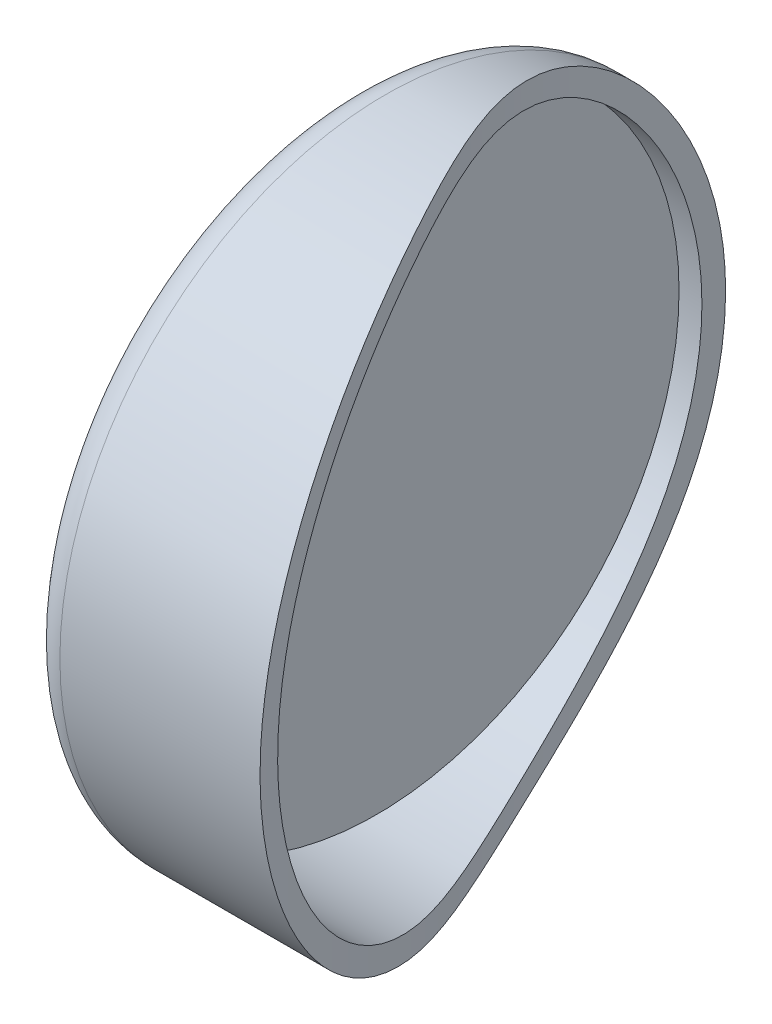
SolidWorks part; units mm, degrees
ref_plane "Front Plane" through (0, 0, 0) normal (0, 0, 1) x (1, 0, 0)
ref_plane "Top Plane" through (0, 0, 0) normal (0, 1, 0) x (1, 0, 0)
ref_plane "Right Plane" through (0, 0, 0) normal (1, 0, 0) x (0, 0, -1)
sketch "Sketch1" plane through (0, 0, 0) normal (1, 0, 0) x (0, 0, -1)
  circle A0 centre (0, 0) radius 70
  dimension "D1" = 140
extrude "Boss-Extrude1" add sketch "Sketch1" along normal blind 50
sketch "Sketch3" plane through (50, 0, 0) normal (1, 0, 0) x (0, 0, -1)
  circle A0 centre (0, 0) radius 65
  dimension "130" = 130
extrude "Cut-Extrude1" cut sketch "Sketch3" against normal blind 45
sketch "Sketch4" plane through (0, 0, 0) normal (0, 1, 0) x (1, 0, 0)
  line L1 (50, 70) -> (0, 70) construction
  line L2 (50, -70) -> (50, 70)
  line L3 (50, 70) -> (10, 70)
  spline S0 degree 3 poles (10, 70) (8.7362, 29.1132) (29.4581, -5.5685) (46.8115, -55.9434) (50, -70) knots 0 0 0 0 0.596241 1 1 1 1
  dimension "D2" = 146.8085
  dimension "D1" = 10
  dimension "D3" = 17.7508
extrude "Cut-Extrude2" cut sketch "Sketch4" against normal mid plane 165
fillet "Fillet2" radius 7 1 edges at (0, 0, -70)
sketch "Sketch5" plane through (0, 0, 0) normal (-1, 0, 0) x (0, 0, 1)
  circle A0 centre (0, 0) radius 50
  dimension "D1" = 100
extrude "Boss-Extrude2" add sketch "Sketch5" along normal blind 2
